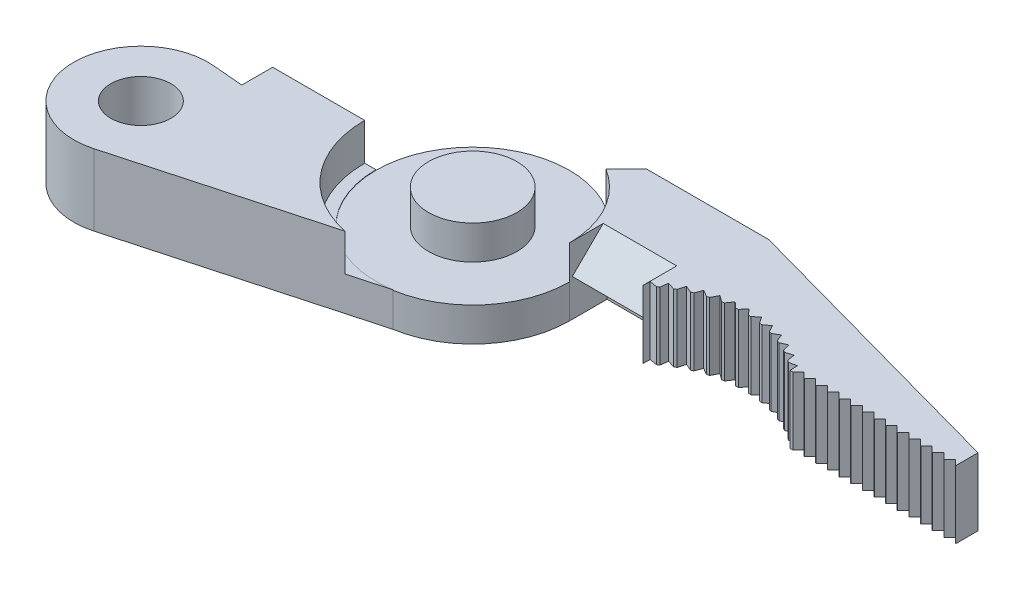
SolidWorks part; units mm, degrees
material "Plain Carbon Steel"
ref_plane "Front Plane" through (0, 0, 0) normal (0, 0, 1) x (1, 0, 0)
ref_plane "Top Plane" through (0, 0, 0) normal (0, 1, 0) x (1, 0, 0)
ref_plane "Right Plane" through (0, 0, 0) normal (1, 0, 0) x (0, 0, -1)
sketch "Sketch1" plane through (0, 0, 0) normal (0, 1, 0) x (1, 0, 0)
  circle A0 centre (0, 0) radius 6.5405
  circle A1 centre (0, 0) radius 2.9845
  dimension "D1" = 13.081
  dimension "D2" = 5.969
extrude "Boss-Extrude1" add sketch "Sketch1" along normal blind 4.826
sketch "Sketch2" plane through (0, 0, 0) normal (0, 1, 0) x (1, 0, 0)
  line L0 (-6.5405, 0) -> (-13.5255, 0)
  line L1 (-13.5255, 0) -> (-13.5255, -2.0885)
  line L2 (-15.6061, -1.9065) -> (-13.5255, -2.0885)
  line L3 (1.0584, -6.4543) -> (-14.798, -10.8125)
  circle A1 centre (-16.002, -6.4321) radius 2.032
  arc A3 (-15.6061, -1.9065) -> (-14.798, -10.8125) centre (-16.002, -6.4321) ccw
  arc A4 (-6.5405, 0) -> (1.0584, -6.4543) centre (0, 0) ccw
  dimension "D1" = 4.064
  dimension "D6" = 16.002
  dimension "D7" = 1.0584
  dimension "D3" = 4.5429
  dimension "D4" = 6.5405
  dimension "D2" = 6.985
  dimension "D5" = 85
extrude "Boss-Extrude2" add sketch "Sketch2" along normal up to surface (4.826 mm away) up to face at (0, 4.826, 6.5405)
hole_wizard "#42 (0.0935) Diameter Hole1" positions "Sketch6" profile "Sketch7" hole size "#42" standard "ANSI Inch"
sketch "Sketch6" plane through (0, 0, 0) normal (0, 0, -1) x (-1, 0, 0)
  line L0 (13.5255, 4.826) -> (13.5255, 0) construction
  line L1 (6.5405, 0) -> (13.5255, 0) construction
  point P0 (10.033, 2.413)
  dimension "D1" = 3.4925
  dimension "D2" = 2.413
sketch "Sketch7" plane through (-10.033, 2.413, 0) normal (1, 0, 0) x (0, 1, 0)
  line L0 (0, 0) -> (0, 2.7455)
  line L1 (0, 2.7455) -> (1.1874, 2.032)
  line L2 (1.1874, 2.032) -> (1.1874, 0)
  line L5 (1.1874, 0) -> (0, 0)
  line L10 (0, 2.7455) -> (-1.1875, 2.032) construction
  line L11 (0, -6.35) -> (0, 107.95) construction
  dimension "Hole Dia." = 2.3749
  dimension "Hole Depth" = 2.032
  dimension "Drill Angle" = 118
sketch "Sketch8" plane through (0, 0, 0) normal (0, 1, 0) x (1, 0, 0)
  line L0 (13.081, 6.9342) -> (32.639, 1.524)
  line L1 (32.639, 1.524) -> (32.639, 0)
  line L2 (32.639, 0) -> (21.463, 0)
  line L3 (13.081, 6.9342) -> (4.7936, 6.9342)
  line L4 (4.7936, 6.9342) -> (3.429, 5.5696)
  line L5 (6.5405, 0) -> (11.557, 0)
  arc A2 (1.0584, -6.4543) -> (-6.5405, 0) centre (0, 0) ccw construction
  arc A4 (21.463, 0) -> (11.557, 0) centre (16.51, -5.7907) ccw
  arc A5 (6.5405, 0) -> (3.429, 5.5696) centre (0, 0) ccw
  point P11 (0, 0)
  dimension "D1" = 11.176
  dimension "D8" = 7.62
  dimension "D2" = 1.524
  dimension "D3" = 5.4102
  dimension "D4" = 32.639
  dimension "D5" = 225
  dimension "D6" = 19.558
  dimension "D7" = 16.51
  dimension "D9" = 3.429
extrude "Boss-Extrude3" add sketch "Sketch8" along normal up to surface (4.826 mm away) up to face at (-10.2144, 4.826, 2.2554)
sketch "Sketch9" plane through (0, 4.826, 0) normal (0, 1, 0) x (1, 0, 0)
  line L10 (-7.3025, 0) -> (-6.5405, 0)
  line L11 (-1.4779, -7.1514) -> (1.567, -6.35)
  line L12 (-14.798, -10.8125) -> (1.0584, -6.4543) construction
  line L32 (33.401, -0.762) -> (33.401, 2.1048)
  arc A4 (-7.3025, 0) -> (-1.4779, -7.1514) centre (0, 0) ccw
  arc A5 (-6.5405, 0) -> (1.567, -6.35) centre (0, 0) ccw
  arc A6 (3.429, 5.5696) -> (-6.5405, 0) centre (0, 0) ccw construction
  arc A7 (1.0584, -6.4543) -> (6.5405, 0) centre (0, 0) ccw construction
  point P0 (0, 0)
  line M26 (-6.5405, 0) -> (-13.5255, 0)
  line M30 (-14.798, -10.8125) -> (1.0584, -6.4543)
  dimension "D1" = 7.3025
  dimension "D2" = 6.5405
  dimension "D3" = 6.35
extrude "Cut-Extrude1" cut sketch "Sketch9" against normal blind 2.5082 contours A5 A4 M26 M30
sketch "Sketch10" plane through (0, 4.826, 0) normal (0, 1, 0) x (1, 0, 0)
  line L0 (32.639, 0) -> (32.258, 0.381)
  line L1 (32.258, 0.381) -> (31.877, 0)
  line L3 (21.463, 0) -> (32.639, 0) construction
  line L4 (31.877, 0) -> (32.639, 0)
  dimension "D1" = 0.381
extrude "Cut-Extrude2" cut sketch "Sketch10" against normal through all
pattern_linear "LPattern1" count 14 spacing 0.7874 along (-1, 0, 0) of "Cut-Extrude2"
sketch "Sketch11" plane through (0, 4.826, 0) normal (0, 1, 0) x (1, 0, 0)
  line L0 (21.463, 0) -> (21.438, 0.5125)
  line L1 (21.438, 0.5125) -> (20.9346, 0.4131)
  arc A0 (21.463, 0) -> (11.557, 0) centre (16.51, -5.7907) ccw construction
  arc A1 (21.463, 0) -> (20.9346, 0.4131) centre (16.51, -5.7907) ccw
  dimension "D1" = 8.001
extrude "Cut-Extrude3" cut sketch "Sketch11" against normal through all
pattern_circular "CirPattern1" count 13 over 76.5 about axis through (16.51, 0, 5.7907) along (0, 1, 0) of "Cut-Extrude3"
sketch "Sketch13" plane through (0, 4.826, 0) normal (0, 1, 0) x (1, 0, 0)
  line L0 (11.5121, 0) -> (11.5121, 2.54)
  line L1 (11.5121, 2.54) -> (6.5405, 2.54)
  line L2 (6.5405, 2.54) -> (6.5405, 0)
  line L3 (6.5405, 0) -> (11.5121, 0)
  point P3 (0, 0)
  point P7 (11.4935, 0)
  dimension "D1" = 2.54
extrude "Cut-Extrude5" cut sketch "Sketch13" against normal blind 2.5082
sketch "Sketch14" plane through (6.5405, 0, 0) normal (1, 0, 0) x (0, 0, -1)
  line L0 (0, 2.3178) -> (2.54, 4.826)
  line L1 (2.54, 4.826) -> (2.54, 2.3177)
  line L2 (2.54, 2.3177) -> (2.54, 4.826) construction
  line L3 (2.54, 2.3177) -> (0, 2.3177) construction
  line L4 (2.54, 2.3177) -> (0, 2.3178)
extrude "Boss-Extrude4" add sketch "Sketch14" along normal up to next
sketch "Sketch15" plane through (0, 0, 0) normal (0, -1, 0) x (1, 0, 0)
  line L0 (6.5405, 0) -> (6.5405, -2.54)
  line L1 (6.5405, 0) -> (11.5121, 0) construction
  line L2 (6.5405, -2.54) -> (11.5121, -2.54)
  line L3 (11.5121, -2.54) -> (11.5121, 0)
  line L4 (11.5121, 0) -> (6.5405, 0)
  arc A0 (6.5405, 0) -> (1.0584, 6.4543) centre (0, 0) ccw construction
  point P7 (0, 0)
  dimension "D1" = 2.54
extrude "Cut-Extrude6" cut sketch "Sketch15" against normal blind 2.5082
sketch "Sketch16" plane through (0, 4.826, 0) normal (0, 1, 0) x (1, 0, 0)
  circle A0 centre (0, 0) radius 6.5405
extrude "Cut-Extrude7" cut sketch "Sketch16" against normal blind 2.54
sketch "Sketch18" plane through (0, 0, 0) normal (0, 1, 0) x (1, 0, 0)
  circle A0 centre (0, 0) radius 2.9845
  dimension "D1" = 5.969
extrude "Boss-Extrude5" add sketch "Sketch18" along normal blind 4.572
sketch "Sketch19" plane through (0, 4.826, 0) normal (0, 1, 0) x (1, 0, 0)
  line L76 (6.5405, 0) -> (6.5405, 2.54)
  line L77 (6.5405, 2.54) -> (11.5121, 2.54)
  line L78 (11.5121, 2.54) -> (11.5121, 0)
  line L80 (11.5121, 0) -> (11.5313, 0.4726)
  line L81 (11.5313, 0.4726) -> (12.0356, 0.3773)
  line L82 (12.1799, 0.4794) -> (12.2576, 0.9867)
  line L83 (12.2576, 0.9867) -> (12.7481, 0.8359)
  line L84 (12.9029, 0.9215) -> (13.0364, 1.4169)
  line L85 (13.0364, 1.4169) -> (13.5071, 1.2127)
  line L86 (13.6705, 1.2805) -> (13.8582, 1.7581)
  line L87 (13.8582, 1.7581) -> (14.3033, 1.5028)
  line L88 (14.4732, 1.552) -> (14.7128, 2.0058)
  line L89 (14.7128, 2.0058) -> (15.1268, 1.7027)
  line L90 (15.3011, 1.7328) -> (15.5896, 2.1572)
  line L91 (15.5896, 2.1572) -> (15.9674, 1.81)
  line L92 (16.1439, 1.8205) -> (16.4777, 2.2102)
  line L93 (16.4777, 2.2102) -> (16.8147, 1.8232)
  line L94 (16.9913, 1.8141) -> (17.3663, 2.1643)
  line L95 (17.3663, 2.1643) -> (17.6582, 1.7423)
  line L96 (17.8327, 1.7136) -> (18.2443, 2.0201)
  line L97 (18.2443, 2.0201) -> (18.4875, 1.5682)
  line L98 (18.6578, 1.5203) -> (19.1009, 1.7792)
  line L99 (19.1009, 1.7792) -> (19.2924, 1.3031)
  line L100 (19.4563, 1.2367) -> (19.9254, 1.4447)
  line L101 (19.9254, 1.4447) -> (20.0629, 0.9503)
  line L102 (20.2184, 0.8661) -> (20.7076, 1.0207)
  line L103 (20.7076, 1.0207) -> (20.7894, 0.5142)
  line L104 (20.9346, 0.4131) -> (21.438, 0.5125)
  line L105 (21.438, 0.5125) -> (21.463, 0)
  line L106 (21.463, 0) -> (21.6408, 0)
  line L107 (21.6408, 0) -> (22.0218, 0.381)
  line L108 (22.0218, 0.381) -> (22.4028, 0)
  line L109 (22.4028, 0) -> (22.4282, 0)
  line L110 (22.4282, 0) -> (22.8092, 0.381)
  line L111 (22.8092, 0.381) -> (23.1902, 0)
  line L112 (23.1902, 0) -> (23.2156, 0)
  line L113 (23.2156, 0) -> (23.5966, 0.381)
  line L114 (23.5966, 0.381) -> (23.9776, 0)
  line L115 (23.9776, 0) -> (24.003, 0)
  line L116 (24.003, 0) -> (24.384, 0.381)
  line L117 (24.384, 0.381) -> (24.765, 0)
  line L118 (24.765, 0) -> (24.7904, 0)
  line L119 (24.7904, 0) -> (25.1714, 0.381)
  line L120 (25.1714, 0.381) -> (25.5524, 0)
  line L121 (25.5524, 0) -> (25.5778, 0)
  line L122 (25.5778, 0) -> (25.9588, 0.381)
  line L123 (25.9588, 0.381) -> (26.3398, 0)
  line L124 (26.3398, 0) -> (26.3652, 0)
  line L125 (26.3652, 0) -> (26.7462, 0.381)
  line L126 (26.7462, 0.381) -> (27.1272, 0)
  line L127 (27.1272, 0) -> (27.1526, 0)
  line L128 (27.1526, 0) -> (27.5336, 0.381)
  line L129 (27.5336, 0.381) -> (27.9146, 0)
  line L130 (27.9146, 0) -> (27.94, 0)
  line L131 (27.94, 0) -> (28.321, 0.381)
  line L132 (28.321, 0.381) -> (28.702, 0)
  line L133 (28.702, 0) -> (28.7274, 0)
  line L134 (28.7274, 0) -> (29.1084, 0.381)
  line L135 (29.1084, 0.381) -> (29.4894, 0)
  line L136 (29.4894, 0) -> (29.5148, 0)
  line L137 (29.5148, 0) -> (29.8958, 0.381)
  line L138 (29.8958, 0.381) -> (30.2768, 0)
  line L139 (30.2768, 0) -> (30.3022, 0)
  line L140 (30.3022, 0) -> (30.6832, 0.381)
  line L141 (30.6832, 0.381) -> (31.0642, 0)
  line L142 (31.0642, 0) -> (31.0896, 0)
  line L143 (31.0896, 0) -> (31.4706, 0.381)
  line L144 (31.4706, 0.381) -> (31.8516, 0)
  line L145 (31.8516, 0) -> (31.877, 0)
  line L146 (31.877, 0) -> (32.258, 0.381)
  line L147 (32.258, 0.381) -> (32.639, 0)
  line L148 (32.639, 0) -> (32.639, 1.524)
  line L149 (32.639, 1.524) -> (13.081, 6.9342)
  line L150 (13.081, 6.9342) -> (4.7936, 6.9342)
  line L151 (4.7936, 6.9342) -> (3.429, 5.5696)
  line L152 (6.5405, 0) -> (6.5405, 2.54)
  line L153 (6.5405, 2.54) -> (11.5121, 2.54)
  line L154 (11.5121, 2.54) -> (11.5121, 0)
  line L156 (11.5121, 0) -> (11.5313, 0.4726)
  line L157 (11.5313, 0.4726) -> (12.0356, 0.3773)
  line L158 (12.1799, 0.4794) -> (12.2576, 0.9867)
  line L159 (12.2576, 0.9867) -> (12.7481, 0.8359)
  line L160 (12.9029, 0.9215) -> (13.0364, 1.4169)
  line L161 (13.0364, 1.4169) -> (13.5071, 1.2127)
  line L162 (13.6705, 1.2805) -> (13.8582, 1.7581)
  line L163 (13.8582, 1.7581) -> (14.3033, 1.5028)
  line L164 (14.4732, 1.552) -> (14.7128, 2.0058)
  line L165 (14.7128, 2.0058) -> (15.1268, 1.7027)
  line L166 (15.3011, 1.7328) -> (15.5896, 2.1572)
  line L167 (15.5896, 2.1572) -> (15.9674, 1.81)
  line L168 (16.1439, 1.8205) -> (16.4777, 2.2102)
  line L169 (16.4777, 2.2102) -> (16.8147, 1.8232)
  line L170 (16.9913, 1.8141) -> (17.3663, 2.1643)
  line L171 (17.3663, 2.1643) -> (17.6582, 1.7423)
  line L172 (17.8327, 1.7136) -> (18.2443, 2.0201)
  line L173 (18.2443, 2.0201) -> (18.4875, 1.5682)
  line L174 (18.6578, 1.5203) -> (19.1009, 1.7792)
  line L175 (19.1009, 1.7792) -> (19.2924, 1.3031)
  line L176 (19.4563, 1.2367) -> (19.9254, 1.4447)
  line L177 (19.9254, 1.4447) -> (20.0629, 0.9503)
  line L178 (20.2184, 0.8661) -> (20.7076, 1.0207)
  line L179 (20.7076, 1.0207) -> (20.7894, 0.5142)
  line L180 (20.9346, 0.4131) -> (21.438, 0.5125)
  line L181 (21.438, 0.5125) -> (21.463, 0)
  line L182 (21.463, 0) -> (21.6408, 0)
  line L183 (21.6408, 0) -> (22.0218, 0.381)
  line L184 (22.0218, 0.381) -> (22.4028, 0)
  line L185 (22.4028, 0) -> (22.4282, 0)
  line L186 (22.4282, 0) -> (22.8092, 0.381)
  line L187 (22.8092, 0.381) -> (23.1902, 0)
  line L188 (23.1902, 0) -> (23.2156, 0)
  line L189 (23.2156, 0) -> (23.5966, 0.381)
  line L190 (23.5966, 0.381) -> (23.9776, 0)
  line L191 (23.9776, 0) -> (24.003, 0)
  line L192 (24.003, 0) -> (24.384, 0.381)
  line L193 (24.384, 0.381) -> (24.765, 0)
  line L194 (24.765, 0) -> (24.7904, 0)
  line L195 (24.7904, 0) -> (25.1714, 0.381)
  line L196 (25.1714, 0.381) -> (25.5524, 0)
  line L197 (25.5524, 0) -> (25.5778, 0)
  line L198 (25.5778, 0) -> (25.9588, 0.381)
  line L199 (25.9588, 0.381) -> (26.3398, 0)
  line L200 (26.3398, 0) -> (26.3652, 0)
  line L201 (26.3652, 0) -> (26.7462, 0.381)
  line L202 (26.7462, 0.381) -> (27.1272, 0)
  line L203 (27.1272, 0) -> (27.1526, 0)
  line L204 (27.1526, 0) -> (27.5336, 0.381)
  line L205 (27.5336, 0.381) -> (27.9146, 0)
  line L206 (27.9146, 0) -> (27.94, 0)
  line L207 (27.94, 0) -> (28.321, 0.381)
  line L208 (28.321, 0.381) -> (28.702, 0)
  line L209 (28.702, 0) -> (28.7274, 0)
  line L210 (28.7274, 0) -> (29.1084, 0.381)
  line L211 (29.1084, 0.381) -> (29.4894, 0)
  line L212 (29.4894, 0) -> (29.5148, 0)
  line L213 (29.5148, 0) -> (29.8958, 0.381)
  line L214 (29.8958, 0.381) -> (30.2768, 0)
  line L215 (30.2768, 0) -> (30.3022, 0)
  line L216 (30.3022, 0) -> (30.6832, 0.381)
  line L217 (30.6832, 0.381) -> (31.0642, 0)
  line L218 (31.0642, 0) -> (31.0896, 0)
  line L219 (31.0896, 0) -> (31.4706, 0.381)
  line L220 (31.4706, 0.381) -> (31.8516, 0)
  line L221 (31.8516, 0) -> (31.877, 0)
  line L222 (31.877, 0) -> (32.258, 0.381)
  line L223 (32.258, 0.381) -> (32.639, 0)
  line L224 (32.639, 0) -> (32.639, 1.524)
  line L225 (32.639, 1.524) -> (13.081, 6.9342)
  line L226 (13.081, 6.9342) -> (4.7936, 6.9342)
  line L227 (4.7936, 6.9342) -> (3.429, 5.5696)
  arc A13 (6.5405, 0) -> (3.429, 5.5696) centre (0, 0) ccw
  arc A14 (12.1799, 0.4794) -> (12.0356, 0.3773) centre (16.51, -5.7907) ccw
  arc A15 (12.9029, 0.9215) -> (12.7481, 0.8359) centre (16.51, -5.7907) ccw
  arc A16 (13.6705, 1.2805) -> (13.5071, 1.2127) centre (16.51, -5.7907) ccw
  arc A17 (14.4732, 1.552) -> (14.3033, 1.5028) centre (16.51, -5.7907) ccw
  arc A18 (15.3011, 1.7328) -> (15.1268, 1.7027) centre (16.51, -5.7907) ccw
  arc A19 (16.1439, 1.8205) -> (15.9674, 1.81) centre (16.51, -5.7907) ccw
  arc A20 (16.9913, 1.8141) -> (16.8147, 1.8232) centre (16.51, -5.7907) ccw
  arc A21 (17.8327, 1.7136) -> (17.6582, 1.7423) centre (16.51, -5.7907) ccw
  arc A22 (18.6578, 1.5203) -> (18.4875, 1.5682) centre (16.51, -5.7907) ccw
  arc A23 (19.4563, 1.2367) -> (19.2924, 1.3031) centre (16.51, -5.7907) ccw
  arc A24 (20.2184, 0.8661) -> (20.0629, 0.9503) centre (16.51, -5.7907) ccw
  arc A25 (20.9346, 0.4131) -> (20.7894, 0.5142) centre (16.51, -5.7907) ccw
  arc A26 (6.5405, 0) -> (3.429, 5.5696) centre (0, 0) ccw
  arc A27 (12.1799, 0.4794) -> (12.0356, 0.3773) centre (16.51, -5.7907) ccw
  arc A28 (12.9029, 0.9215) -> (12.7481, 0.8359) centre (16.51, -5.7907) ccw
  arc A29 (13.6705, 1.2805) -> (13.5071, 1.2127) centre (16.51, -5.7907) ccw
  arc A30 (14.4732, 1.552) -> (14.3033, 1.5028) centre (16.51, -5.7907) ccw
  arc A31 (15.3011, 1.7328) -> (15.1268, 1.7027) centre (16.51, -5.7907) ccw
  arc A32 (16.1439, 1.8205) -> (15.9674, 1.81) centre (16.51, -5.7907) ccw
  arc A33 (16.9913, 1.8141) -> (16.8147, 1.8232) centre (16.51, -5.7907) ccw
  arc A34 (17.8327, 1.7136) -> (17.6582, 1.7423) centre (16.51, -5.7907) ccw
  arc A35 (18.6578, 1.5203) -> (18.4875, 1.5682) centre (16.51, -5.7907) ccw
  arc A36 (19.4563, 1.2367) -> (19.2924, 1.3031) centre (16.51, -5.7907) ccw
  arc A37 (20.2184, 0.8661) -> (20.0629, 0.9503) centre (16.51, -5.7907) ccw
  arc A38 (20.9346, 0.4131) -> (20.7894, 0.5142) centre (16.51, -5.7907) ccw
  dimension "D1" = 0
extrude "Cut-Extrude8" cut sketch "Sketch19" against normal blind 0.254
sketch "Sketch20" plane through (11.5121, 0, 0) normal (1, 0, 0) x (0, 0, -1)
  line L0 (2.54, 4.826) -> (2.2828, 4.572)
  line L1 (2.2828, 4.572) -> (2.54, 4.572)
  line L2 (2.54, 4.572) -> (2.54, 4.826)
extrude "Cut-Extrude9" cut sketch "Sketch20" against normal up to next
